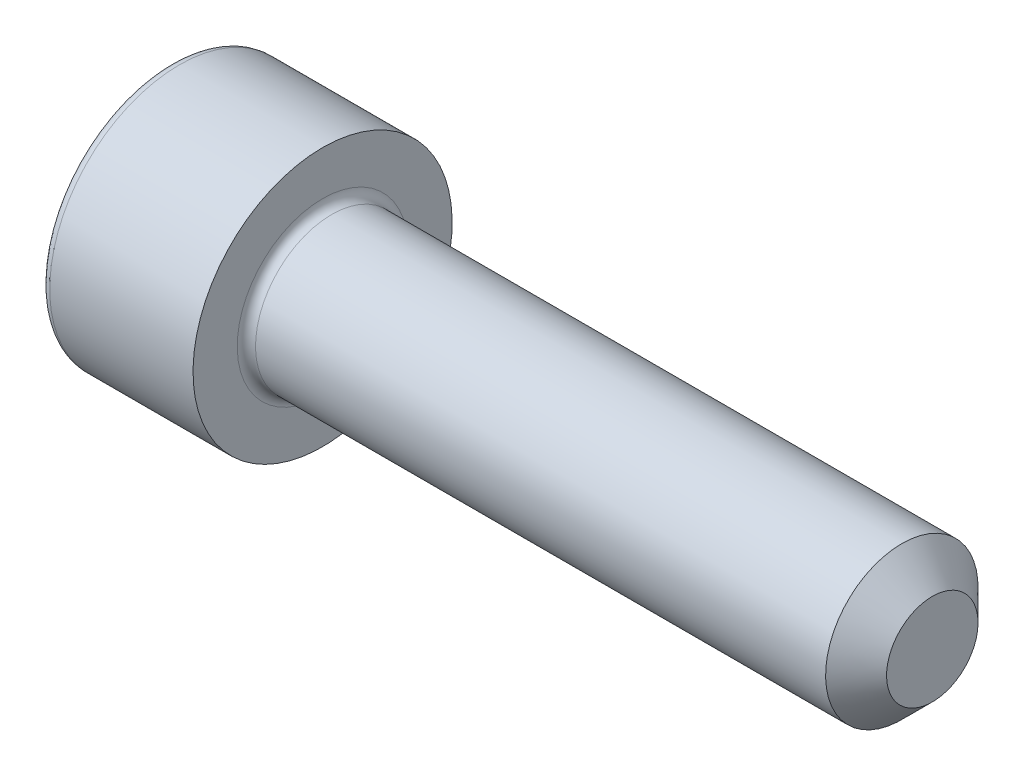
SolidWorks part; units mm, degrees
ref_plane "Спереди" through (0, 0, 0) normal (0, 0, 1) x (1, 0, 0)
ref_plane "Сверху" through (0, 0, 0) normal (0, 1, 0) x (1, 0, 0)
ref_plane "Справа" through (0, 0, 0) normal (1, 0, 0) x (0, 0, -1)
sketch "Эскиз1" plane through (0, 0, 0) normal (0, 0, 1) x (1, 0, 0)
  line L0 (0, 0) -> (0, 4.25)
  line L1 (0, 4.25) -> (5, 4.25)
  line L2 (5, 4.25) -> (5, 2.5)
  line L3 (5, 2.5) -> (25, 2.5)
  line L4 (25, 2.5) -> (25, 0)
  line L5 (25, 0) -> (0, 0) construction
  line L6 (0, 0) -> (25, 0)
  dimension "D1" = 8.5
  dimension "D2" = 5
  dimension "D3" = 5
  dimension "D4" = 20
revolve "Повернуть1" add sketch "Эскиз1" angle 360 about L5
cosmetic thread "Условное изображение резьбы1" parameters "D2"=4.11
sketch "Эскиз2" plane through (0, 0, 0) normal (-1, 0, 0) x (0, 0, 1)
  line L1 (-1.1547, 2) -> (-2.3094, 0)
  line L2 (-2.3094, 0) -> (-1.1547, -2)
  line L3 (-1.1547, -2) -> (1.1547, -2)
  line L4 (1.1547, -2) -> (2.3094, 0)
  line L5 (2.3094, 0) -> (1.1547, 2)
  line L6 (1.1547, 2) -> (-1.1547, 2)
  circle A0 centre (0, 0) radius 2 construction
  dimension "D1" = 4
extrude "Вырез-Вытянуть1" cut sketch "Эскиз2" against normal blind 2.5
fillet "Скругление1" radius 0.3 2 edges at (0, 4.25, 0) (5, 2.5, 0)
chamfer "Фаска1" distance 1 angle 45 1 edges at (25, 2.5, 0)
